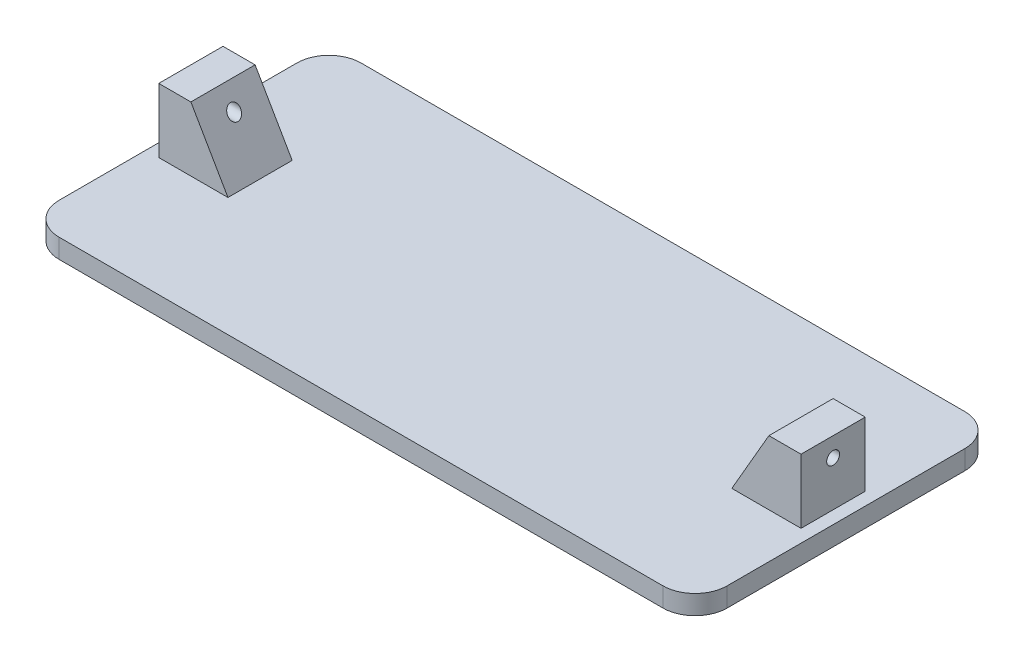
SolidWorks part; units mm, degrees
ref_plane "Спереди" through (0, 0, 0) normal (0, 0, 1) x (1, 0, 0)
ref_plane "Сверху" through (0, 0, 0) normal (0, 1, 0) x (1, 0, 0)
ref_plane "Справа" through (0, 0, 0) normal (1, 0, 0) x (0, 0, -1)
sketch "Эскиз1" plane through (0, 0, 0) normal (0, 1, 0) x (1, 0, 0)
  line L1 (-45, -21.5) -> (45, -21.5)
  line L2 (-50, -16.5) -> (-50, 16.5)
  line L3 (-45, 21.5) -> (45, 21.5)
  line L4 (50, -16.5) -> (50, 16.5)
  line L5 (-50, -21.5) -> (50, 21.5) construction
  line L6 (-50, 21.5) -> (50, -21.5) construction
  arc A0 (50, 16.5) -> (45, 21.5) centre (45, 16.5) ccw
  arc A1 (45, -21.5) -> (50, -16.5) centre (45, -16.5) ccw
  arc A2 (-50, -16.5) -> (-45, -21.5) centre (-45, -16.5) ccw
  arc A3 (-45, 21.5) -> (-50, 16.5) centre (-45, 16.5) ccw
  point P0 (0, 0)
  dimension "D3" = 5
  dimension "D1" = 100
  dimension "D2" = 43
extrude "Бобышка-Вытянуть1" add sketch "Эскиз1" along normal blind 3
sketch "Эскиз3" plane through (0, 0, 0) normal (0, 0, 1) x (1, 0, 0)
  line L0 (-45, 3) -> (-50, 3) construction
  line L1 (-45, 3) -> (-50, 3)
  line L2 (50, 3) -> (45, 3) construction
  line L3 (50, 3) -> (45, 3)
  line L4 (-50, 3) -> (-50, 13)
  line L5 (-50, 13) -> (-45, 13)
  line L6 (-45, 13) -> (-39.2265, 3)
  line L7 (-39.2265, 3) -> (-45, 3)
  line L8 (0, 13.7665) -> (0, -12.3638) construction
  line L9 (39.2265, 3) -> (45, 3)
  line L10 (45, 13) -> (39.2265, 3)
  line L11 (50, 13) -> (45, 13)
  line L12 (50, 3) -> (50, 13)
  line L13 (45, 3) -> (50, 3)
  dimension "D1" = 10
  dimension "D2" = 5
  dimension "D3" = 60
extrude "Бобышка-Вытянуть2" add sketch "Эскиз3" along normal mid plane 10 contours L7 L6 L5 L4 L1 | L3 L12 L11 L10 L9
sketch "Эскиз4" plane through (-50, 0, 0) normal (-1, 0, 0) x (0, 0, 1)
  line L0 (5, 3) -> (16.5, 3) construction
  line L1 (5, 3) -> (16.5, 3)
  line L2 (0, 0) -> (0, 13) construction
  line L3 (-16.5, 0) -> (16.5, 0) construction
  line L4 (5, 13) -> (-5, 13) construction
  line L5 (-5, 3) -> (-5, 13) construction
  line L6 (-5, 3) -> (-5, 13)
  circle A0 centre (0, 10) radius 1
  dimension "D1" = 2
  dimension "D2" = 10
extrude "Вырез-Вытянуть1" cut sketch "Эскиз4" against normal through all contours A0 | A0 L2
sketch "Эскиз5" plane through (0, 0, 0) normal (0, -1, 0) x (1, 0, 0)
  line L0 (52, -16.5) -> (52, 16.5)
  line L1 (45, 23.5) -> (-45, 23.5)
  line L2 (-52, 16.5) -> (-52, -16.5)
  line L3 (-45, -23.5) -> (45, -23.5)
  line L4 (50, -16.5) -> (50, 16.5)
  line L5 (45, 21.5) -> (-45, 21.5)
  line L6 (-50, 16.5) -> (-50, -16.5)
  line L7 (-45, -21.5) -> (45, -21.5)
  line L8 (50, -16.5) -> (50, 16.5)
  line L9 (45, 21.5) -> (-45, 21.5)
  line L10 (-50, 16.5) -> (-50, -16.5)
  line L11 (-45, -21.5) -> (45, -21.5)
  line L12 (-52, -16.5) -> (-52, -18.5)
  line L13 (-47, -23.5) -> (-45, -23.5)
  line L14 (45, -23.5) -> (47, -23.5)
  line L15 (52, -18.5) -> (52, -16.5)
  line L16 (45, 23.5) -> (47, 23.5)
  line L17 (52, 18.5) -> (52, 16.5)
  line L18 (-45, 23.5) -> (-47, 23.5)
  line L19 (-52, 18.5) -> (-52, 16.5)
  arc A0 (52, -18.5) -> (47, -23.5) centre (47, -18.5) cw
  arc A1 (52, 18.5) -> (47, 23.5) centre (47, 18.5) ccw
  arc A2 (-47, 23.5) -> (-52, 18.5) centre (-47, 18.5) ccw
  arc A3 (-52, -18.5) -> (-47, -23.5) centre (-47, -18.5) ccw
  arc A4 (45, -21.5) -> (50, -16.5) centre (45, -16.5) ccw
  arc A5 (50, 16.5) -> (45, 21.5) centre (45, 16.5) ccw
  arc A6 (-45, 21.5) -> (-50, 16.5) centre (-45, 16.5) ccw
  arc A7 (-50, -16.5) -> (-45, -21.5) centre (-45, -16.5) ccw
  arc A8 (45, -21.5) -> (50, -16.5) centre (45, -16.5) ccw
  arc A9 (50, 16.5) -> (45, 21.5) centre (45, 16.5) ccw
  arc A10 (-45, 21.5) -> (-50, 16.5) centre (-45, 16.5) ccw
  arc A11 (-50, -16.5) -> (-45, -21.5) centre (-45, -16.5) ccw
  arc A16 (-45, 23.5) -> (-52, 16.5) centre (-45, 16.5) ccw construction
  arc A17 (-52, -16.5) -> (-45, -23.5) centre (-45, -16.5) ccw construction
  arc A18 (45, -23.5) -> (52, -16.5) centre (45, -16.5) ccw construction
  arc A19 (52, 16.5) -> (45, 23.5) centre (45, 16.5) ccw construction
  dimension "D3" = 5
  dimension "D1" = 0
  dimension "D2" = 2
extrude "Бобышка-Вытянуть3" add sketch "Эскиз5" against normal blind 3
